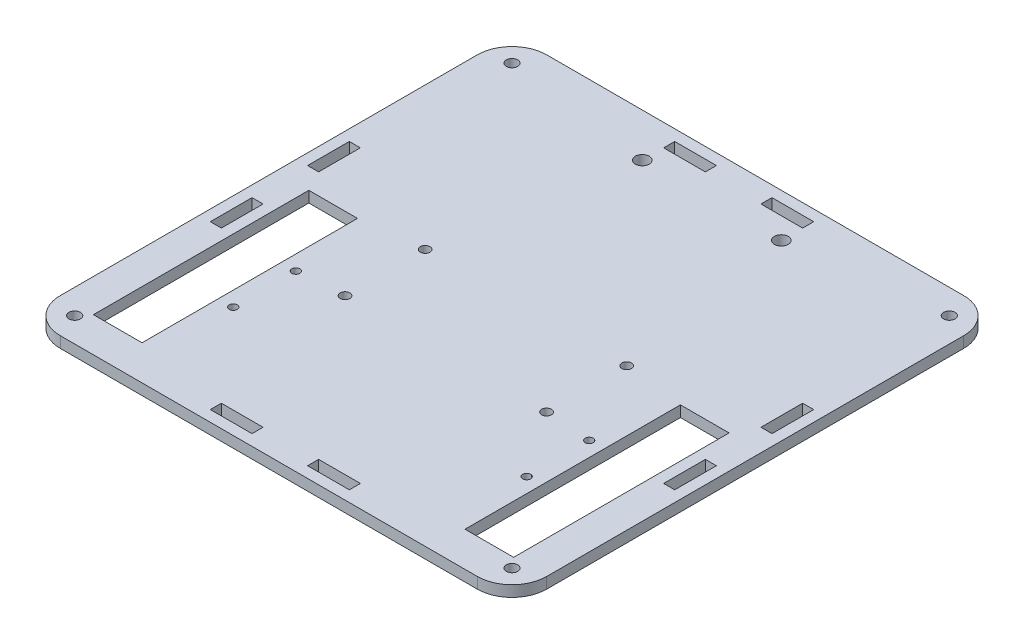
SolidWorks part; units mm, degrees
ref_plane "Front Plane" through (0, 0, 0) normal (0, 0, 1) x (1, 0, 0)
ref_plane "Top Plane" through (0, 0, 0) normal (0, 1, 0) x (1, 0, 0)
ref_plane "Right Plane" through (0, 0, 0) normal (1, 0, 0) x (0, 0, -1)
sketch "Sketch1" plane through (0, 0, 0) normal (0, 1, 0) x (1, 0, 0)
  line L0 (-70, 0) -> (70, 0) construction
  line L1 (-70, 70) -> (70, 70)
  line L2 (-70, 70) -> (-70, -70)
  line L3 (-70, -70) -> (70, -70)
  line L4 (70, 70) -> (70, -70)
  line L5 (-60.475, 2) -> (-60.475, -60)
  line L6 (-46.475, -60) -> (-60.475, -60)
  line L7 (-32.5, 7.5) -> (32.5, 7.5)
  line L8 (-32.5, 7.5) -> (-32.5, -22.5)
  line L9 (-32.5, -22.5) -> (32.5, -22.5)
  line L10 (32.5, 7.5) -> (32.5, -22.5)
  line L11 (0, 70) -> (0, -70) construction
  line L12 (46.475, 2) -> (60.475, 2)
  line L13 (-29, 4) -> (29, 4)
  line L14 (-29, 4) -> (-29, -19.05)
  line L15 (-29, -19.05) -> (29, -19.05)
  line L16 (29, 4) -> (29, -19.05)
  line L17 (46.475, 2) -> (46.475, -60)
  line L18 (46.475, -60) -> (60.475, -60)
  line L19 (60.475, 2) -> (60.475, -60)
  line L20 (-46.475, 2) -> (-46.475, -60)
  line L21 (-46.475, 2) -> (-60.475, 2)
  line L22 (-66.825, -8) -> (-66.825, -20)
  line L23 (63.65, -8) -> (66.825, -8)
  line L24 (63.65, -8) -> (63.65, -20)
  line L25 (63.65, -20) -> (66.825, -20)
  line L26 (66.825, -8) -> (66.825, -20)
  line L27 (8, -66.825) -> (20, -66.825)
  line L28 (8, -66.825) -> (8, -63.65)
  line L29 (8, -63.65) -> (20, -63.65)
  line L30 (20, -66.825) -> (20, -63.65)
  line L31 (-63.65, -20) -> (-66.825, -20)
  line L32 (-63.65, -8) -> (-63.65, -20)
  line L33 (-63.65, -8) -> (-66.825, -8)
  line L34 (-20, -66.825) -> (-20, -63.65)
  line L35 (-8, -63.65) -> (-20, -63.65)
  line L36 (-8, -66.825) -> (-8, -63.65)
  line L37 (-8, -66.825) -> (-20, -66.825)
  line L38 (66.825, 8) -> (66.825, 20)
  line L39 (63.65, 20) -> (66.825, 20)
  line L40 (63.65, 8) -> (63.65, 20)
  line L41 (63.65, 8) -> (66.825, 8)
  line L42 (20, 66.825) -> (20, 63.65)
  line L43 (8, 63.65) -> (20, 63.65)
  line L44 (8, 66.825) -> (8, 63.65)
  line L45 (8, 66.825) -> (20, 66.825)
  line L46 (-8, 66.825) -> (-20, 66.825)
  line L47 (-8, 66.825) -> (-8, 63.65)
  line L48 (-8, 63.65) -> (-20, 63.65)
  line L49 (-20, 66.825) -> (-20, 63.65)
  line L50 (-63.65, 8) -> (-66.825, 8)
  line L51 (-63.65, 8) -> (-63.65, 20)
  line L52 (-63.65, 20) -> (-66.825, 20)
  line L53 (-66.825, 8) -> (-66.825, 20)
  line L54 (-70, -70) -> (70, 70) construction
  line L55 (-70, 70) -> (70, -70) construction
  circle A0 centre (29, 4) radius 1.4
  circle A1 centre (29, -19.05) radius 1.4
  circle A2 centre (-29, -19.05) radius 1.4
  circle A3 centre (-29, 4) radius 1.4
  circle A4 centre (42.225, -20) radius 1.15
  circle A5 centre (42.225, -38) radius 1.15
  circle A6 centre (-42.225, -38) radius 1.15
  circle A7 centre (-42.225, -20) radius 1.15
  circle A8 centre (20, 57.5) radius 2
  circle A9 centre (-20, 57.5) radius 2
  circle A10 centre (62.9289, -62.9289) radius 1.65
  circle A11 centre (62.9289, 62.9289) radius 1.65
  circle A12 centre (-62.9289, -62.9289) radius 1.65
  circle A13 centre (-62.9289, 62.9289) radius 1.65
  point P0 (0, 0)
  point P11 (0, 0)
  dimension "D5" = 2.8
  dimension "D6" = 2.3
  dimension "D18" = 4
  dimension "D27" = 3.3
  dimension "D1" = 65
  dimension "D2" = 30
  dimension "D3" = 58
  dimension "D4" = 23.05
  dimension "D7" = 18
  dimension "D9" = 4.25
  dimension "D10" = 14
  dimension "D11" = 62
  dimension "D8" = 22
  dimension "D12" = 9.525
  dimension "D13" = 140
  dimension "D14" = 140
  dimension "D16" = 3.5
  dimension "D17" = 3.5
  dimension "D19" = 20
  dimension "D21" = 3.175
  dimension "D22" = 12
  dimension "D23" = 12
  dimension "D24" = 8
  dimension "D25" = 8
  dimension "D26" = 10
  dimension "D28" = 10
  dimension "D15" = 12.5
  dimension "D29" = 4
  dimension "D30" = 3.175
  dimension "D20" = 3.175
  dimension "D31" = 3.175
extrude "Boss-Extrude1" add sketch "Sketch1" along normal blind 3.175 contours L4 L1 L2 L3 A6 A5 A4 L21 L20 L6 L5 L7 L10 L9 L8 L12 L19 L18 L17 A7 | L10 L7 L8 L9 L13 A9 A8 A0 L16 A1 L15 A2 L14 A3 | L13 A9 A3 L14 A2 L15 A1 L16 A0 A8
fillet "Fillet1" radius 10 4 edges at (70, 1.5875, -70) (70, 1.5875, 70) (-70, 1.5875, 70) (-70, 1.5875, -70)
equation "\"D8@Sketch1\"=(\"D11@Sketch1\"-\"D7@Sketch1\")/2"
